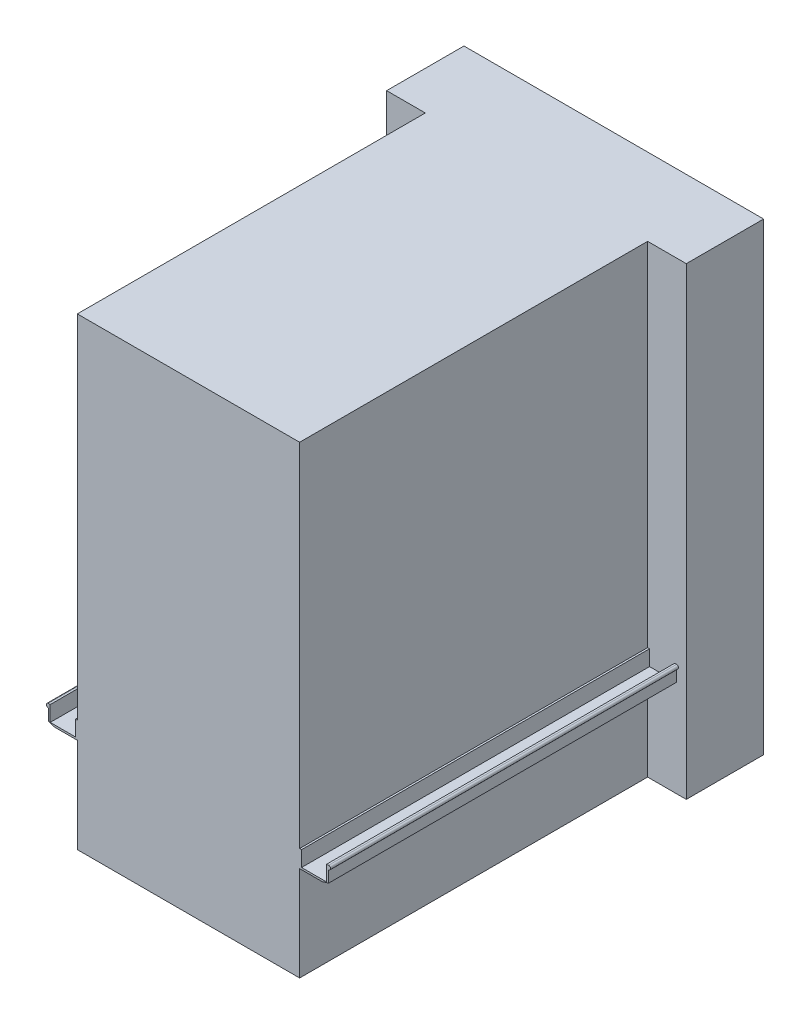
SolidWorks part; units mm, degrees
ref_plane "前基準面" through (0, 0, 0) normal (0, 0, 1) x (1, 0, 0)
ref_plane "上基準面" through (0, 0, 0) normal (0, 1, 0) x (1, 0, 0)
ref_plane "右基準面" through (0, 0, 0) normal (1, 0, 0) x (0, 0, -1)
sketch "草圖1" plane through (0, 0, 0) normal (0, 0, 1) x (1, 0, 0)
  line L0 (-725, 309.4582) -> (-725, 249.4582)
  line L1 (608.7081, 249.409) -> (608.7081, 239.4582) construction
  line L2 (584.9508, 329.4582) -> (575, 329.4582)
  line L3 (725, 329.4582) -> (715.0492, 329.4582)
  line L4 (715.0492, 249.409) -> (584.9508, 249.409)
  line L5 (584.9508, 329.4582) -> (584.9508, 249.409)
  line L6 (715.0492, 329.4582) -> (715.0492, 249.409)
  line L7 (-725, 249.4582) -> (-692.0261, 239.4582)
  line L8 (-692.0261, 239.4582) -> (-575, 239.4582)
  line L9 (-575, 239.4582) -> (-575, -250.5418)
  line L10 (-608.7081, 249.409) -> (-608.7081, 239.4582) construction
  line L11 (-715.0492, 329.4582) -> (-715.0492, 249.409)
  line L12 (-584.9508, 329.4582) -> (-584.9508, 249.409)
  line L13 (-715.0492, 249.409) -> (-584.9508, 249.409)
  line L14 (-725, 329.4582) -> (-715.0492, 329.4582)
  line L15 (-584.9508, 329.4582) -> (-575, 329.4582)
  line L16 (0, 2585.9131) -> (0, -269.0275)
  line L18 (692.0261, 239.4582) -> (575, 239.4582)
  line L19 (725, 249.4582) -> (692.0261, 239.4582)
  line L20 (725, 309.4582) -> (725, 249.4582)
  line L21 (575, 239.4582) -> (575, -250.5418)
  line L22 (-575, 2149.4582) -> (575, 2149.4582)
  line L23 (-575, 2149.4582) -> (-575, 329.4582)
  line L24 (-575, -250.5418) -> (575, -250.5418)
  line L25 (575, 2149.4582) -> (575, 329.4582)
  line L26 (-575, 2149.4582) -> (575, -250.5418) construction
  line L27 (-575, -250.5418) -> (575, 2149.4582) construction
  arc A0 (-725, 329.4582) -> (-725, 309.4582) centre (-725, 319.4582) ccw
  arc A1 (725, 329.4582) -> (725, 309.4582) centre (725, 319.4582) cw
  point P29 (0, 949.4582)
  dimension "D2" = 10
  dimension "D1" = 90
  dimension "D3" = 60
  dimension "D4" = 490
  dimension "D5" = 2400
  dimension "D6" = 1150
extrude "填料-伸長1" add sketch "草圖1" along normal blind 1800 contours L14 A0 L0 L7 L8 L9 L24 L16 L22 L23 L15 L12 L13 L11 | A1 L3 L6 L4 L5 L2 L25 L22 L16 L24 L21 L18 L19 L20
sketch "草圖2" plane through (0, 0, 0) normal (0, 0, -1) x (-1, 0, 0)
  line L0 (0, -250.5418) -> (0, 2149.4582) construction
  line L1 (775, 2149.4582) -> (-775, 2149.4582)
  line L2 (-775, 2149.4582) -> (-775, -250.5418)
  line L3 (-775, -250.5418) -> (775, -250.5418)
  line L4 (775, 2149.4582) -> (775, -250.5418)
  line L5 (575, -250.5418) -> (-575, -250.5418) construction
  line L6 (575, 2149.4582) -> (-575, 2149.4582) construction
  line L7 (-725, 309.4582) -> (-725, 249.4582) construction
  line L8 (725, 309.4582) -> (725, 249.4582) construction
  dimension "D1" = 50
  dimension "D2" = 50
extrude "填料-伸長2" add sketch "草圖2" along normal blind 400
